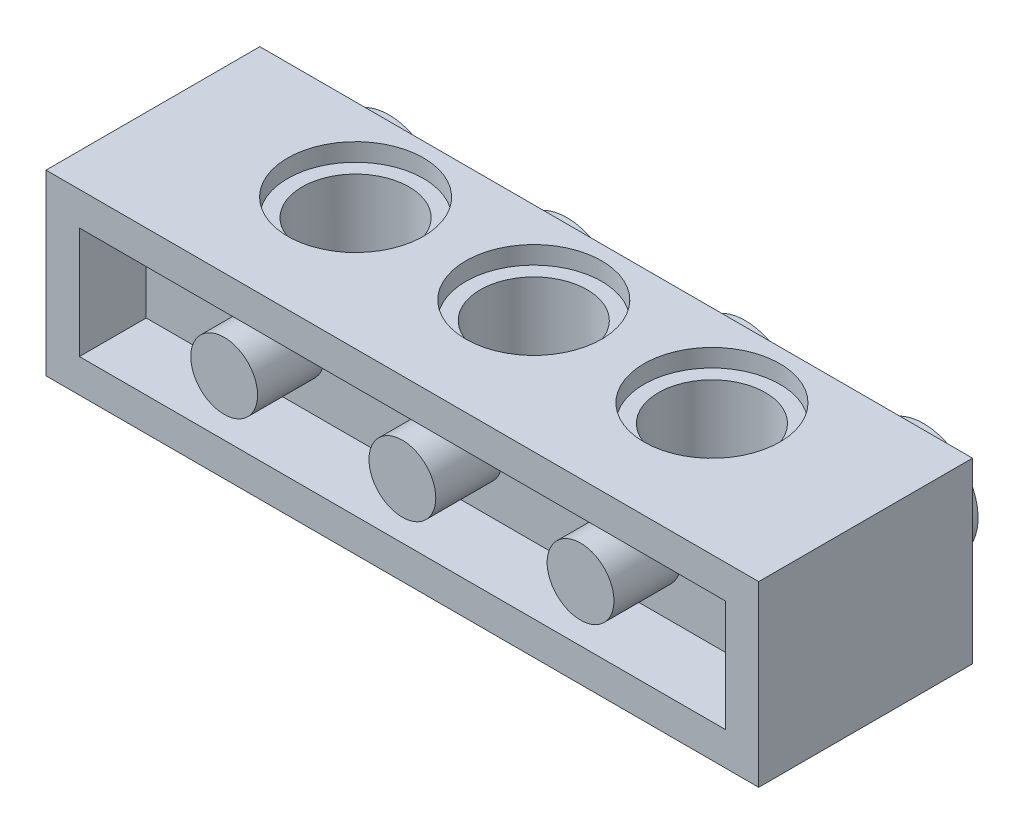
SolidWorks part; units mm, degrees
ref_plane "Front Plane" through (0, 0, 0) normal (0, 0, 1) x (1, 0, 0)
ref_plane "Top Plane" through (0, 0, 0) normal (0, 1, 0) x (1, 0, 0)
ref_plane "Right Plane" through (0, 0, 0) normal (1, 0, 0) x (0, 0, -1)
sketch "Sketch1" plane through (0, 0, 0) normal (0, 1, 0) x (1, 0, 0)
  line L1 (-16, 3.7) -> (16, 3.7)
  line L2 (-16, -5.9) -> (-16, 3.7)
  line L3 (16, -5.9) -> (16, 3.7)
  line L4 (-16, -5.9) -> (16, -5.9)
  point P20 (8, -3.7)
  point P25 (-8, -3.7)
  dimension "D1" = 9.6
  dimension "D2" = 32
extrude "Boss-Extrude3" add sketch "Sketch1" along normal blind 8 contours L2 L1 L3 L4
sketch "Sketch2" plane through (0, 8, 0) normal (0, 1, 0) x (1, 0, 0)
  circle A0 centre (0, 0) radius 2.4
  circle A2 centre (8, 0) radius 2.4
  circle A9 centre (-8, 0) radius 2.4
  dimension "D1" = 8
  dimension "D2" = 4.8
extrude "Cut-Extrude6" cut sketch "Sketch2" against normal blind 7.8
sketch "Sketch3" plane through (0, 8, 0) normal (0, 1, 0) x (1, 0, 0)
  circle A0 centre (0, 0) radius 3.05
  circle A1 centre (8, 0) radius 3.05
  circle A4 centre (-8, 0) radius 3.05
  dimension "D1" = 6.1
  dimension "D2" = 8
extrude "Cut-Extrude7" cut sketch "Sketch3" against normal blind 0.8
sketch "Sketch4" plane through (0, 0, 0) normal (0, -1, 0) x (1, 0, 0)
  circle A0 centre (0, 0) radius 3.05
  circle A1 centre (8, 0) radius 3.05
  circle A4 centre (-8, 0) radius 3.05
  dimension "D1" = 8
  dimension "D2" = 6.1
extrude "Cut-Extrude8" cut sketch "Sketch4" against normal blind 0.8
sketch "Sketch5" plane through (0, 0, -3.7) normal (0, 0, -1) x (-1, 0, 0)
  circle A0 centre (-12, 4) radius 2.45
  circle A1 centre (-4, 4) radius 2.45
  circle A2 centre (4, 4) radius 2.45
  circle A3 centre (12, 4) radius 2.45
  dimension "D2" = 4.9
extrude "Boss-Extrude4" add sketch "Sketch5" along normal blind 1.8
sketch "Sketch6" plane through (0, 0, 5.9) normal (0, 0, 1) x (1, 0, 0)
  line L0 (-16, 8) -> (-16, 0) construction
  line L1 (-16, 0) -> (16, 0) construction
  line L9 (-14.5, 6.5) -> (14.5, 6.5)
  line L10 (-14.5, 6.5) -> (-14.5, 1.5)
  line L11 (-14.5, 1.5) -> (14.5, 1.5)
  line L12 (14.5, 6.5) -> (14.5, 1.5)
  dimension "D1" = 1.5
  dimension "D2" = 1.5
  dimension "D3" = 29
  dimension "D4" = 5
extrude "Cut-Extrude9" cut sketch "Sketch6" against normal blind 3
sketch "Sketch7" plane through (0, 0, 2.9) normal (0, 0, 1) x (1, 0, 0)
  circle A0 centre (-8, 4) radius 1.5
  circle A1 centre (0, 4) radius 1.5
  circle A2 centre (8, 4) radius 1.5
  dimension "D1" = 8
  dimension "D2" = 3
extrude "Boss-Extrude5" add sketch "Sketch7" along normal blind 3
